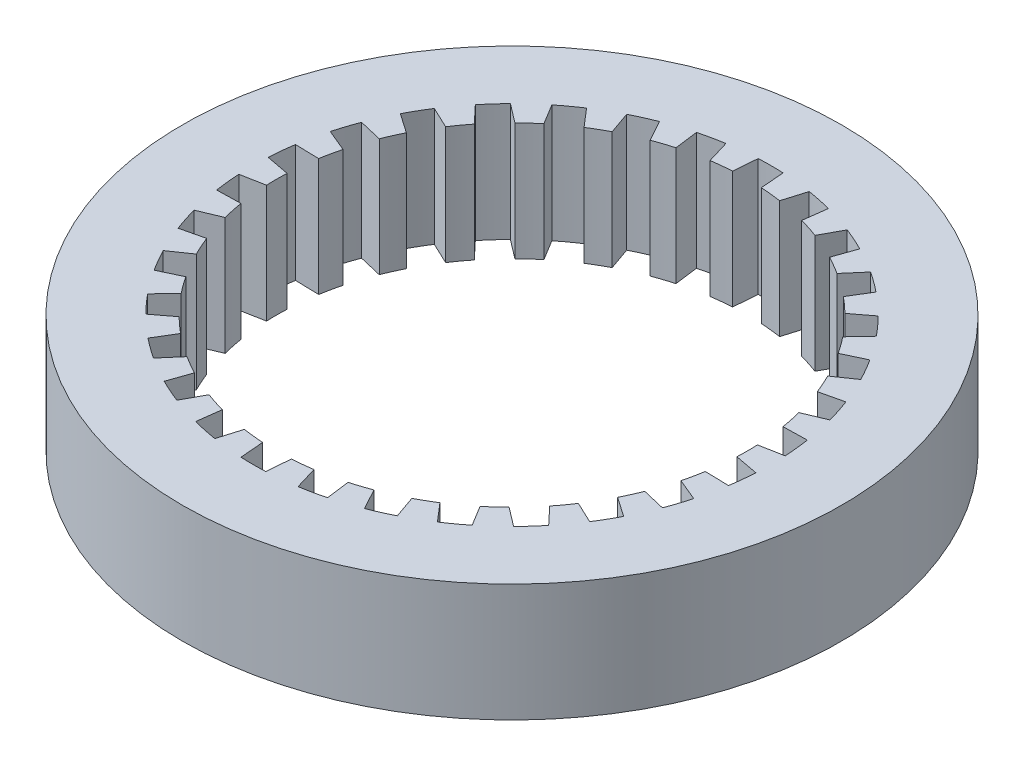
SolidWorks part; units mm, degrees
ref_plane "Front Plane" through (0, 0, 0) normal (0, 0, 1) x (1, 0, 0)
ref_plane "Top Plane" through (0, 0, 0) normal (0, 1, 0) x (1, 0, 0)
ref_plane "Right Plane" through (0, 0, 0) normal (1, 0, 0) x (0, 0, -1)
sketch "Sketch1" plane through (0, 0, 0) normal (0, 1, 0) x (1, 0, 0)
  circle A0 centre (0, 0) radius 17.78
extrude "Boss-Extrude1" add sketch "Sketch1" along normal blind 6.35
sketch "Sketch2" plane through (0, 6.35, 0) normal (0, 1, 0) x (1, 0, 0)
  line L1 (-0.6703, 13.9539) -> (-0.7753, 12.6763)
  line L2 (0.6703, 13.9539) -> (0.7753, 12.6763)
  line L3 (2.2456, 13.7883) -> (1.8772, 12.5605)
  line L4 (3.5568, 13.5096) -> (3.3939, 12.2381)
  line L5 (5.0633, 13.0201) -> (4.4476, 11.8957)
  line L6 (6.2879, 12.4749) -> (5.8642, 11.265)
  line L7 (7.6597, 11.6829) -> (6.8237, 10.7111)
  line L8 (8.7442, 10.895) -> (8.0782, 9.7996)
  line L9 (9.9213, 9.8351) -> (8.9015, 9.0583)
  line L10 (10.8183, 8.8389) -> (9.9391, 7.9059)
  line L11 (11.7493, 7.5574) -> (10.5903, 7.0096)
  line L12 (12.4196, 6.3965) -> (11.3657, 5.6667)
  line L13 (13.0638, 4.9494) -> (11.8163, 4.6546)
  line L14 (13.4781, 3.6745) -> (12.2955, 3.1798)
  line L15 (13.8074, 2.1252) -> (12.5258, 2.0961)
  line L16 (13.9475, 0.792) -> (12.6879, 0.554)
  line L17 (13.9475, -0.792) -> (12.6879, -0.554)
  line L18 (13.8074, -2.1252) -> (12.5258, -2.0961)
  line L19 (13.4781, -3.6745) -> (12.2955, -3.1798)
  line L20 (13.0638, -4.9494) -> (11.8163, -4.6546)
  line L21 (12.4196, -6.3965) -> (11.3657, -5.6667)
  line L22 (11.7493, -7.5574) -> (10.5903, -7.0096)
  line L23 (10.8183, -8.8389) -> (9.9391, -7.9059)
  line L24 (9.9213, -9.8351) -> (8.9015, -9.0583)
  line L25 (8.7442, -10.895) -> (8.0782, -9.7996)
  line L26 (7.6597, -11.6829) -> (6.8237, -10.7111)
  line L27 (6.2879, -12.4749) -> (5.8642, -11.265)
  line L28 (5.0633, -13.0201) -> (4.4476, -11.8957)
  line L29 (3.5568, -13.5096) -> (3.3939, -12.2381)
  line L30 (2.2456, -13.7883) -> (1.8772, -12.5605)
  line L31 (0.6703, -13.9539) -> (0.7753, -12.6763)
  line L32 (-0.6703, -13.9539) -> (-0.7753, -12.6763)
  line L33 (-2.2456, -13.7883) -> (-1.8772, -12.5605)
  line L34 (-3.5568, -13.5096) -> (-3.3939, -12.2381)
  line L35 (-5.0633, -13.0201) -> (-4.4476, -11.8957)
  line L36 (-6.2879, -12.4749) -> (-5.8642, -11.265)
  line L37 (-7.6597, -11.6829) -> (-6.8237, -10.7111)
  line L38 (-8.7442, -10.895) -> (-8.0782, -9.7996)
  line L39 (-9.9213, -9.8351) -> (-8.9015, -9.0583)
  line L40 (-10.8183, -8.8389) -> (-9.9391, -7.9059)
  line L41 (-11.7493, -7.5574) -> (-10.5903, -7.0096)
  line L42 (-12.4196, -6.3965) -> (-11.3657, -5.6667)
  line L43 (-13.0638, -4.9494) -> (-11.8163, -4.6546)
  line L44 (-13.4781, -3.6745) -> (-12.2955, -3.1798)
  line L45 (-13.8074, -2.1252) -> (-12.5258, -2.0961)
  line L46 (-13.9475, -0.792) -> (-12.6879, -0.554)
  line L47 (-13.9475, 0.792) -> (-12.6879, 0.554)
  line L48 (-13.8074, 2.1252) -> (-12.5258, 2.0961)
  line L49 (-13.4781, 3.6745) -> (-12.2955, 3.1798)
  line L50 (-13.0638, 4.9494) -> (-11.8163, 4.6546)
  line L51 (-12.4196, 6.3965) -> (-11.3657, 5.6667)
  line L52 (-11.7493, 7.5574) -> (-10.5903, 7.0096)
  line L53 (-10.8183, 8.8389) -> (-9.9391, 7.9059)
  line L54 (-9.9213, 9.8351) -> (-8.9015, 9.0583)
  line L55 (-8.7442, 10.895) -> (-8.0782, 9.7996)
  line L56 (-7.6597, 11.6829) -> (-6.8237, 10.7111)
  line L57 (-6.2879, 12.4749) -> (-5.8642, 11.265)
  line L58 (-5.0633, 13.0201) -> (-4.4476, 11.8957)
  line L59 (-3.5568, 13.5096) -> (-3.3939, 12.2381)
  line L60 (-2.2456, 13.7883) -> (-1.8772, 12.5605)
  arc A0 (-2.2456, 13.7883) -> (-3.5568, 13.5096) centre (0, 0) ccw
  arc A1 (-0.7753, 12.6763) -> (-1.8772, 12.5605) centre (0, 0) ccw
  arc A2 (10.8183, 8.8389) -> (9.9213, 9.8351) centre (0, 0) ccw
  arc A3 (-7.6597, 11.6829) -> (-8.7442, 10.895) centre (0, 0) ccw
  arc A4 (-5.0633, 13.0201) -> (-6.2879, 12.4749) centre (0, 0) ccw
  arc A5 (0.6703, 13.9539) -> (-0.6703, 13.9539) centre (0, 0) ccw
  arc A6 (3.5568, 13.5096) -> (2.2456, 13.7883) centre (0, 0) ccw
  arc A7 (6.2879, 12.4749) -> (5.0633, 13.0201) centre (0, 0) ccw
  arc A8 (8.7442, 10.895) -> (7.6597, 11.6829) centre (0, 0) ccw
  arc A9 (-9.9213, 9.8351) -> (-10.8183, 8.8389) centre (0, 0) ccw
  arc A10 (-11.7493, 7.5574) -> (-12.4196, 6.3965) centre (0, 0) ccw
  arc A11 (-13.0638, 4.9494) -> (-13.4781, 3.6745) centre (0, 0) ccw
  arc A12 (-11.3657, 5.6667) -> (-11.8163, 4.6546) centre (0, 0) ccw
  arc A13 (-9.9391, 7.9059) -> (-10.5903, 7.0096) centre (0, 0) ccw
  arc A14 (-8.0782, 9.7996) -> (-8.9015, 9.0583) centre (0, 0) ccw
  arc A15 (-5.8642, 11.265) -> (-6.8237, 10.7111) centre (0, 0) ccw
  arc A16 (-3.3939, 12.2381) -> (-4.4476, 11.8957) centre (0, 0) ccw
  arc A17 (1.8772, 12.5605) -> (0.7753, 12.6763) centre (0, 0) ccw
  arc A18 (4.4476, 11.8957) -> (3.3939, 12.2381) centre (0, 0) ccw
  arc A19 (6.8237, 10.7111) -> (5.8642, 11.265) centre (0, 0) ccw
  arc A20 (8.9015, 9.0583) -> (8.0782, 9.7996) centre (0, 0) ccw
  arc A21 (10.5903, 7.0096) -> (9.9391, 7.9059) centre (0, 0) ccw
  arc A22 (12.4196, 6.3965) -> (11.7493, 7.5574) centre (0, 0) ccw
  arc A23 (11.8163, 4.6546) -> (11.3657, 5.6667) centre (0, 0) ccw
  arc A24 (-12.2955, 3.1798) -> (-12.5258, 2.0961) centre (0, 0) ccw
  arc A25 (-13.8074, 2.1252) -> (-13.9475, 0.792) centre (0, 0) ccw
  arc A26 (-12.6879, 0.554) -> (-12.6879, -0.554) centre (0, 0) ccw
  arc A27 (-13.9475, -0.792) -> (-13.8074, -2.1252) centre (0, 0) ccw
  arc A28 (-12.5258, -2.0961) -> (-12.2955, -3.1798) centre (0, 0) ccw
  arc A29 (-13.4781, -3.6745) -> (-13.0638, -4.9494) centre (0, 0) ccw
  arc A30 (-11.8163, -4.6546) -> (-11.3657, -5.6667) centre (0, 0) ccw
  arc A31 (-12.4196, -6.3965) -> (-11.7493, -7.5574) centre (0, 0) ccw
  arc A32 (-10.5903, -7.0096) -> (-9.9391, -7.9059) centre (0, 0) ccw
  arc A33 (-10.8183, -8.8389) -> (-9.9213, -9.8351) centre (0, 0) ccw
  arc A34 (-8.9015, -9.0583) -> (-8.0782, -9.7996) centre (0, 0) ccw
  arc A35 (-8.7442, -10.895) -> (-7.6597, -11.6829) centre (0, 0) ccw
  arc A36 (-6.8237, -10.7111) -> (-5.8642, -11.265) centre (0, 0) ccw
  arc A37 (-6.2879, -12.4749) -> (-5.0633, -13.0201) centre (0, 0) ccw
  arc A38 (-4.4476, -11.8957) -> (-3.3939, -12.2381) centre (0, 0) ccw
  arc A39 (-3.5568, -13.5096) -> (-2.2456, -13.7883) centre (0, 0) ccw
  arc A40 (-1.8772, -12.5605) -> (-0.7753, -12.6763) centre (0, 0) ccw
  arc A41 (-0.6703, -13.9539) -> (0.6703, -13.9539) centre (0, 0) ccw
  arc A42 (0.7753, -12.6763) -> (1.8772, -12.5605) centre (0, 0) ccw
  arc A43 (2.2456, -13.7883) -> (3.5568, -13.5096) centre (0, 0) ccw
  arc A44 (3.3939, -12.2381) -> (4.4476, -11.8957) centre (0, 0) ccw
  arc A45 (5.0633, -13.0201) -> (6.2879, -12.4749) centre (0, 0) ccw
  arc A46 (5.8642, -11.265) -> (6.8237, -10.7111) centre (0, 0) ccw
  arc A47 (7.6597, -11.6829) -> (8.7442, -10.895) centre (0, 0) ccw
  arc A48 (8.0782, -9.7996) -> (8.9015, -9.0583) centre (0, 0) ccw
  arc A49 (9.9213, -9.8351) -> (10.8183, -8.8389) centre (0, 0) ccw
  arc A50 (9.9391, -7.9059) -> (10.5903, -7.0096) centre (0, 0) ccw
  arc A51 (11.7493, -7.5574) -> (12.4196, -6.3965) centre (0, 0) ccw
  arc A52 (11.3657, -5.6667) -> (11.8163, -4.6546) centre (0, 0) ccw
  arc A53 (13.0638, -4.9494) -> (13.4781, -3.6745) centre (0, 0) ccw
  arc A54 (12.2955, -3.1798) -> (12.5258, -2.0961) centre (0, 0) ccw
  arc A55 (13.8074, -2.1252) -> (13.9475, -0.792) centre (0, 0) ccw
  arc A56 (12.6879, -0.554) -> (12.6879, 0.554) centre (0, 0) ccw
  arc A57 (13.9475, 0.792) -> (13.8074, 2.1252) centre (0, 0) ccw
  arc A58 (12.5258, 2.0961) -> (12.2955, 3.1798) centre (0, 0) ccw
  arc A59 (13.4781, 3.6745) -> (13.0638, 4.9494) centre (0, 0) ccw
  point P130 (0, 0)
  dimension "D1" = 30
extrude "Cut-Extrude1" cut sketch "Sketch2" against normal through all contours A13 L52 A10 L51 A12 L50 A11 L49 A24 L48 A25 L47 A26 L46 A27 L45 A28 L44 A29 L43 A30 L42 A31 L41 A32 L40 A33 L39 A34 L38 A35 L37 A36 L36 A37 L35 A38 L34 A39 L33 A40 L32 A41 L31 A42 L30 A43 L29 A44 L28 A45 L27 A46 L26 A47 L25 A48 L24 A49 L23 A50 L22 A51 L21 A52 L20 A53 L19 A54 L18 A55 L17 A56 L16 A57 L15 A58 L14 A59 L13 A23 L12 A22 L11 A21 L10 A2 L9 A20 L8 A8 L7 A19 L6 A7 L5 A18 L4 A6 L3 A17 L2 A5 L1 A1 L60 A0 L59 A16 L58 A4 L57 A15 L56 A3 L55 A14 L54 A9 L53
